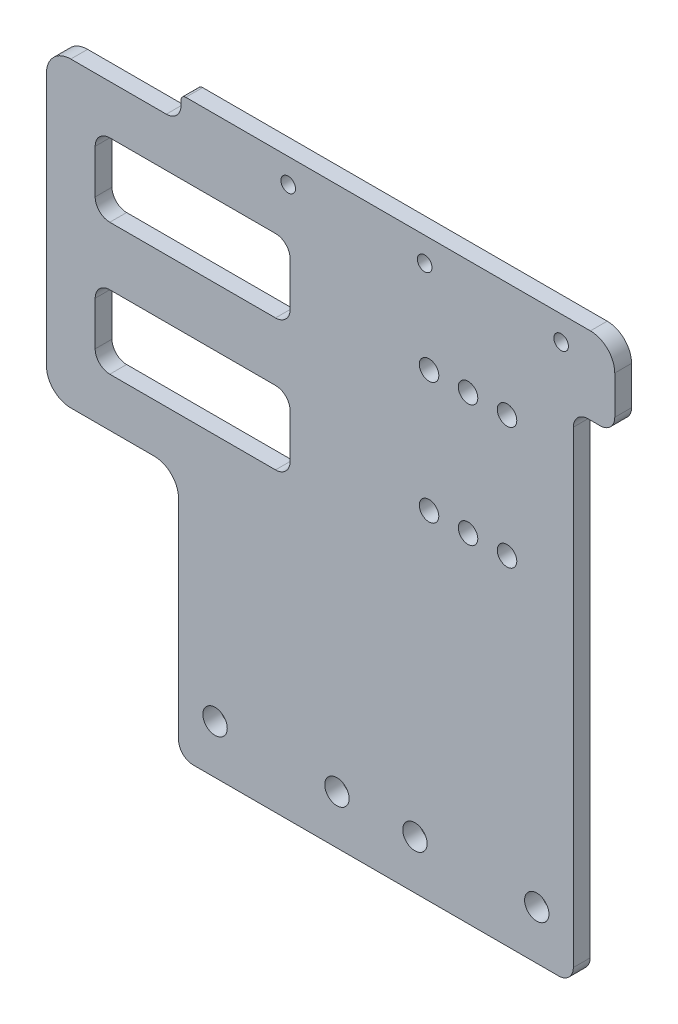
SolidWorks part; units mm, degrees
ref_plane "前视基准面" through (0, 0, 0) normal (0, 0, 1) x (1, 0, 0)
ref_plane "上视基准面" through (0, 0, 0) normal (0, 1, 0) x (1, 0, 0)
ref_plane "右视基准面" through (0, 0, 0) normal (1, 0, 0) x (0, 0, -1)
sketch "Model" plane through (0, 0, 0) normal (0, 0, 1) x (1, 0, 0)
  line L0 (123.5772, 109.5613) -> (123.5772, 117.4257)
  line L1 (37.0772, 4.5456) -> (112.0772, 4.5456)
  line L2 (6.9772, 112.4257) -> (6.9772, 60.4257)
  line L3 (53.9772, 65.4257) -> (19.9772, 65.4257)
  line L4 (53.9772, 80.4257) -> (19.9772, 80.4257)
  line L5 (16.9772, 77.4257) -> (16.9772, 68.4257)
  line L6 (56.9772, 77.4257) -> (56.9772, 68.4257)
  line L7 (120.5772, 106.5613) -> (118.0772, 106.5613)
  line L8 (115.0772, 103.5613) -> (115.0772, 7.5456)
  line L9 (53.9772, 107.4257) -> (19.9772, 107.4257)
  line L10 (53.9772, 92.4257) -> (19.9772, 92.4257)
  line L11 (16.9772, 95.4257) -> (16.9772, 104.4257)
  line L12 (56.9772, 95.4257) -> (56.9772, 104.4257)
  line L13 (35.5772, 122.4257) -> (118.5772, 122.4257)
  line L14 (11.9772, 55.4257) -> (29.0772, 55.4257)
  line L15 (34.0772, 7.5456) -> (34.0772, 50.4257)
  line L16 (85.4772, 86.4257) -> (101.4772, 86.4257) construction
  line L17 (11.9772, 117.4257) -> (31.5772, 117.4257)
  line L18 (34.5772, 120.4257) -> (34.5772, 121.4257)
  circle A0 centre (82.5772, 14.5456) radius 2.5
  circle A1 centre (107.5772, 14.5456) radius 2.5
  arc A2 (120.5772, 106.5613) -> (123.5772, 109.5613) centre (120.5772, 109.5613) ccw
  circle A3 centre (101.4772, 98.9257) radius 2
  circle A4 centre (93.4772, 98.9257) radius 2
  circle A5 centre (85.4772, 98.9257) radius 2
  circle A6 centre (93.4772, 73.9257) radius 2
  circle A7 centre (101.4772, 73.9257) radius 2
  circle A8 centre (85.4772, 73.9257) radius 2
  arc A9 (6.9772, 60.4257) -> (11.9772, 55.4257) centre (11.9772, 60.4257) ccw
  arc A10 (53.9772, 65.4257) -> (56.9772, 68.4257) centre (53.9772, 68.4257) ccw
  arc A11 (56.9772, 77.4257) -> (53.9772, 80.4257) centre (53.9772, 77.4257) ccw
  arc A12 (19.9772, 80.4257) -> (16.9772, 77.4257) centre (19.9772, 77.4257) ccw
  arc A13 (16.9772, 68.4257) -> (19.9772, 65.4257) centre (19.9772, 68.4257) ccw
  circle A14 centre (84.5772, 117.4257) radius 1.5
  circle A15 centre (112.5772, 117.4257) radius 1.5
  circle A16 centre (56.5772, 117.4257) radius 1.5
  arc A17 (56.9772, 104.4257) -> (53.9772, 107.4257) centre (53.9772, 104.4257) ccw
  arc A18 (53.9772, 92.4257) -> (56.9772, 95.4257) centre (53.9772, 95.4257) ccw
  arc A19 (16.9772, 95.4257) -> (19.9772, 92.4257) centre (19.9772, 95.4257) ccw
  arc A20 (19.9772, 107.4257) -> (16.9772, 104.4257) centre (19.9772, 104.4257) ccw
  arc A21 (123.5772, 117.4257) -> (118.5772, 122.4257) centre (118.5772, 117.4257) ccw
  circle A22 centre (41.5772, 14.5456) radius 2.5
  circle A23 centre (66.5772, 14.5456) radius 2.5
  arc A24 (34.0772, 50.4257) -> (29.0772, 55.4257) centre (29.0772, 50.4257) ccw
  arc A25 (118.0772, 106.5613) -> (115.0772, 103.5613) centre (118.0772, 103.5613) ccw
  arc A26 (112.0772, 4.5456) -> (115.0772, 7.5456) centre (112.0772, 7.5456) ccw
  arc A27 (34.0772, 7.5456) -> (37.0772, 4.5456) centre (37.0772, 7.5456) ccw
  arc A28 (11.9772, 117.4257) -> (6.9772, 112.4257) centre (11.9772, 112.4257) ccw
  arc A29 (35.5772, 122.4257) -> (34.5772, 121.4257) centre (35.5772, 121.4257) ccw
  arc A30 (31.5772, 117.4257) -> (34.5772, 120.4257) centre (31.5772, 120.4257) ccw
extrude "凸台-拉伸1" add sketch "Model" along normal blind 3.45
